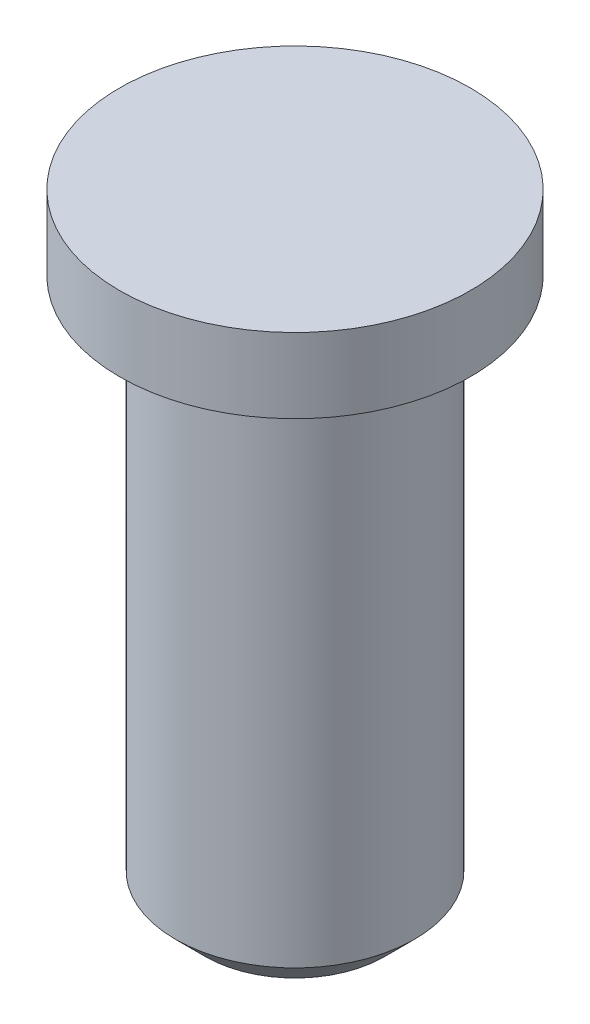
SolidWorks part; units mm, degrees
ref_plane "Front Plane" through (0, 0, 0) normal (0, 0, 1) x (1, 0, 0)
ref_plane "Top Plane" through (0, 0, 0) normal (0, 1, 0) x (1, 0, 0)
ref_plane "Right Plane" through (0, 0, 0) normal (1, 0, 0) x (0, 0, -1)
sketch "Sketch1" plane through (0, 0, 0) normal (0, 1, 0) x (1, 0, 0)
  circle A0 centre (0, 0) radius 8
  dimension "D1" = 16
extrude "Boss-Extrude1" add sketch "Sketch1" along normal blind 36.5
chamfer "Chamfer1" distance 2 angle 45 1 edges at (0, 0, 8)
sketch "Sketch2" plane through (0, 36.5, 0) normal (0, 1, 0) x (1, 0, 0)
  circle A0 centre (0, 0) radius 11.75
  dimension "D1" = 23.5
extrude "Boss-Extrude2" add sketch "Sketch2" along normal blind 5
